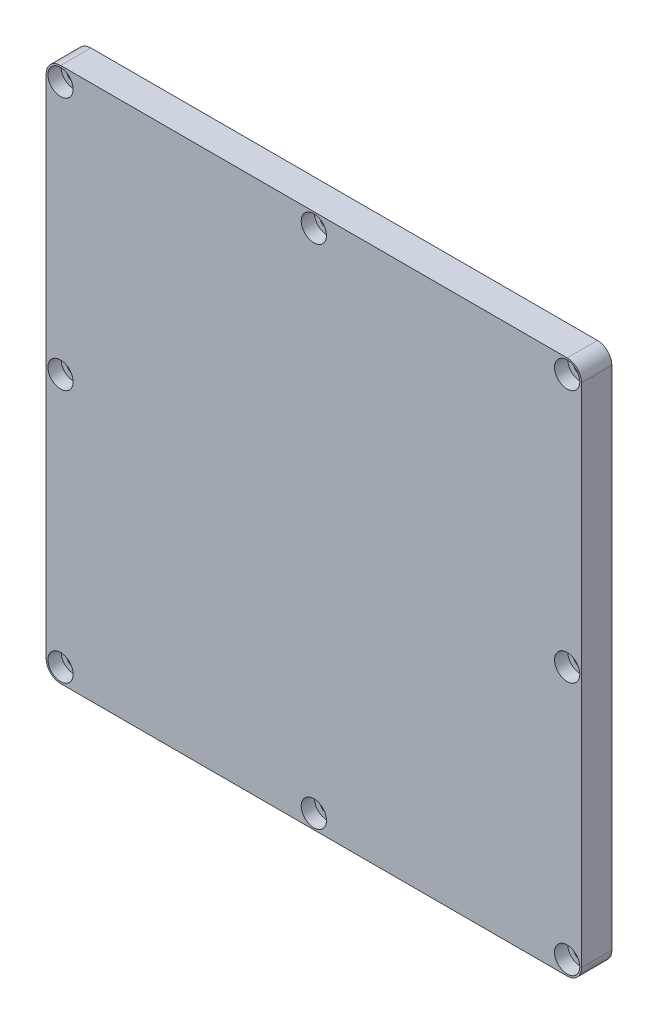
SolidWorks part; units mm, degrees
material "Al 6061-T6"
ref_plane "Front Plane" through (0, 0, 0) normal (0, 0, 1) x (1, 0, 0)
ref_plane "Top Plane" through (0, 0, 0) normal (0, 1, 0) x (1, 0, 0)
ref_plane "Right Plane" through (0, 0, 0) normal (1, 0, 0) x (0, 0, -1)
sketch "Sketch1" plane through (0, 0, 0) normal (0, 0, 1) x (1, 0, 0)
  line L1 (84.1375, -84.1375) -> (-84.1375, -84.1375)
  line L2 (84.1375, -84.1375) -> (84.1375, 84.1375)
  line L3 (84.1375, 84.1375) -> (-84.1375, 84.1375)
  line L4 (-84.1375, -84.1375) -> (-84.1375, 84.1375)
  line L5 (84.1375, -84.1375) -> (-84.1375, 84.1375) construction
  line L6 (84.1375, 84.1375) -> (-84.1375, -84.1375) construction
  point P0 (0, 0)
  dimension "D1" = 168.275
  dimension "D2" = 168.275
extrude "Boss-Extrude1" add sketch "Sketch1" along normal blind 9.525
hole_wizard "CBORE for #8 Socket Head Cap Screw1" positions "Sketch2" profile "Sketch3" counterbore size "#8" standard "ANSI Inch"
sketch "Sketch2" plane through (0, 0, 9.525) normal (0, 0, 1) x (1, 0, 0)
  line L8 (-84.1375, 84.1375) -> (-84.1375, -84.1375)
  line L9 (-84.1375, -84.1375) -> (84.1375, -84.1375)
  line L10 (84.1375, -84.1375) -> (84.1375, 84.1375)
  line L11 (84.1375, 84.1375) -> (-84.1375, 84.1375)
  line L12 (-84.1375, 84.1375) -> (-84.1375, -84.1375)
  line L13 (-84.1375, -84.1375) -> (84.1375, -84.1375)
  line L14 (84.1375, -84.1375) -> (84.1375, 84.1375)
  line L15 (84.1375, 84.1375) -> (-84.1375, 84.1375)
  line L16 (0, 84.1375) -> (0, -84.1375) construction
  line L17 (-84.1375, 0) -> (84.1375, 0) construction
  point P0 (-79.629, 79.629)
  point P32 (0, 79.629)
  point P33 (79.629, 79.629)
  point P34 (0, 0) [skipped]
  point P35 (79.629, 0)
  point P36 (0, -79.629)
  point P37 (79.629, -79.629)
  point P38 (-79.629, 0)
  point P39 (-79.629, -79.629)
  dimension "D2" = 79.629
  dimension "D3" = 79.629
  dimension "D1" = 0
  dimension "D4" = 3
  dimension "D5" = 3
sketch "Sketch3" plane through (-79.629, 79.629, 9.525) normal (1, 0, 0) x (0, -1, 0)
  line L0 (0, 0) -> (0, 9.525)
  line L1 (0, 9.525) -> (2.2479, 9.525)
  line L3 (2.2479, 9.525) -> (2.2479, 4.1656)
  line L4 (2.2479, 4.1656) -> (3.9688, 4.1656)
  line L5 (3.9688, 4.1656) -> (3.9688, 0)
  line L7 (3.9688, 0) -> (0, 0)
  line L11 (0, -6.35) -> (0, 107.95) construction
  dimension "Thru Hole Dia." = 4.4958
  dimension "Thru Hole Depth" = 9.525
  dimension "C'Bore Dia." = 7.9375
  dimension "C'Bore Depth" = 4.1656
fillet "Fillet1" radius 4.5212 4 edges at (-84.1375, -84.1375, 4.7625) (84.1375, -84.1375, 4.7625) (-84.1375, 84.1375, 4.7625) (84.1375, 84.1375, 4.7625)
